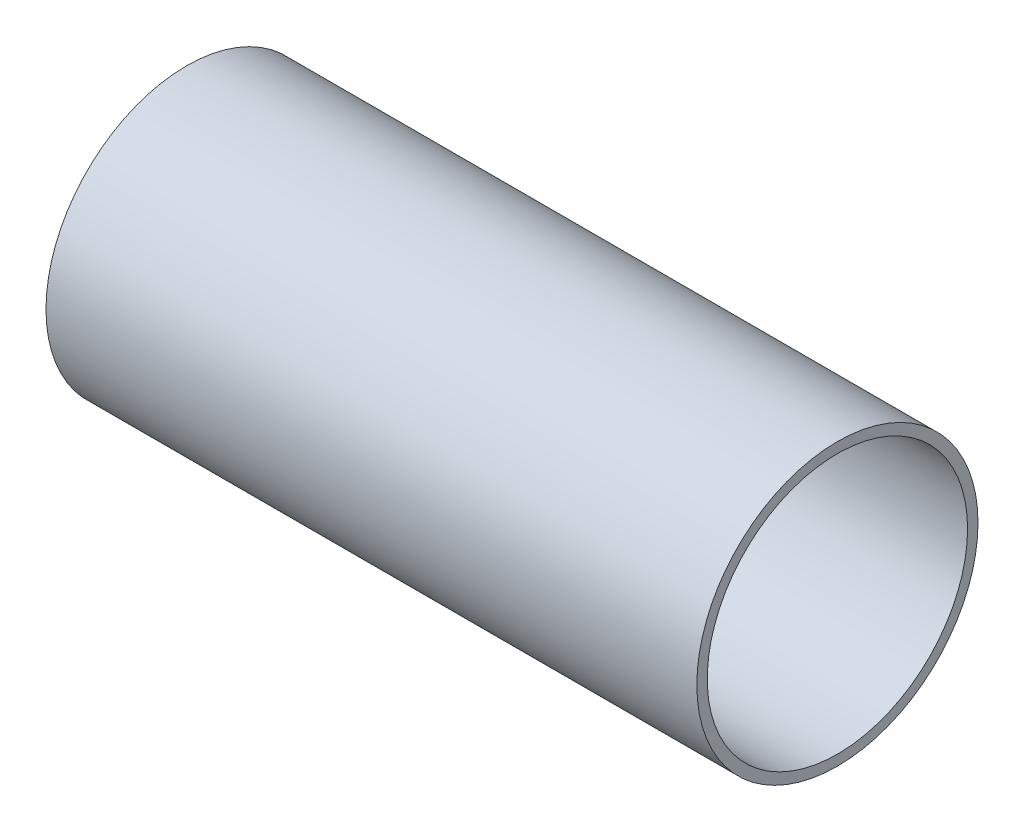
SolidWorks part; units mm, degrees
ref_plane "Front Plane" through (0, 0, 0) normal (0, 0, 1) x (1, 0, 0)
ref_plane "Top Plane" through (0, 0, 0) normal (0, 1, 0) x (1, 0, 0)
ref_plane "Right Plane" through (0, 0, 0) normal (1, 0, 0) x (0, 0, -1)
sketch "Sketch1" plane through (0, 0, 0) normal (1, 0, 0) x (0, 0, -1)
  circle A0 centre (0, 0) radius 25
  circle A1 centre (0, 0) radius 27
  dimension "D1" = 50
  dimension "D2" = 54
extrude "Boss-Extrude1" add sketch "Sketch1" along normal blind 125
